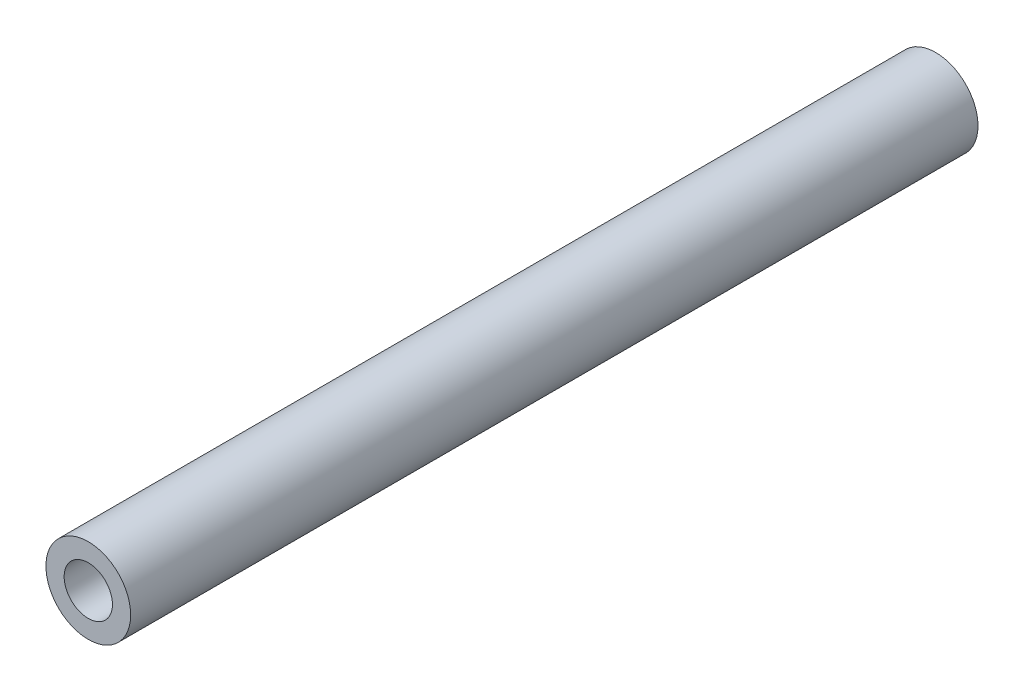
SolidWorks part; units mm, degrees
ref_plane "Plano frontal" through (0, 0, 0) normal (0, 0, 1) x (1, 0, 0)
ref_plane "Plano superior" through (0, 0, 0) normal (0, 1, 0) x (1, 0, 0)
ref_plane "Plano direito" through (0, 0, 0) normal (1, 0, 0) x (0, 0, -1)
sketch "Esboço1" plane through (0, 0, 0) normal (0, 0, 1) x (1, 0, 0)
  circle A0 centre (0, 0) radius 5
  circle A1 centre (0, 0) radius 2.85
  dimension "D1" = 5.7
  dimension "D2" = 10
extrude "Ressalto-extrusão1" add sketch "Esboço1" along normal blind 100
